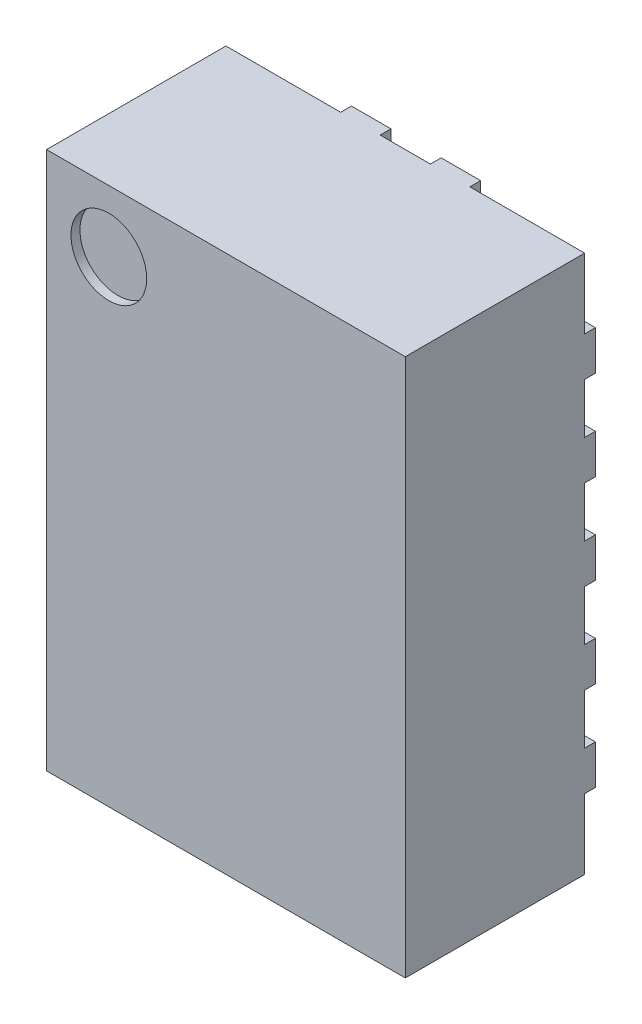
SolidWorks part; units mm, degrees
ref_plane "Front Plane" through (0, 0, 0) normal (0, 0, 1) x (1, 0, 0)
ref_plane "Top Plane" through (0, 0, 0) normal (0, 1, 0) x (1, 0, 0)
ref_plane "Right Plane" through (0, 0, 0) normal (1, 0, 0) x (0, 0, -1)
sketch "Sketch1" plane through (0, 0, 0) normal (0, 0, 1) x (1, 0, 0)
  line L1 (-1, -1.5) -> (1, -1.5)
  line L2 (-1, -1.5) -> (-1, 1.5)
  line L3 (-1, 1.5) -> (1, 1.5)
  line L4 (1, -1.5) -> (1, 1.5)
  line L5 (0, 1.5) -> (0, -1.5) construction
  line L6 (-1, 0) -> (1, 0) construction
  point P0 (0, 0)
  dimension "D1" = 2
  dimension "D2" = 3
extrude "Boss-Extrude1" add sketch "Sketch1" along normal blind 1 from offset 0.06
sketch "Sketch2" plane through (0, 0, 1.06) normal (0, 0, 1) x (1, 0, 0)
  circle A0 centre (-0.653, 1.1551) radius 0.2111
sketch "Sketch3" plane through (0, 0, 0.06) normal (0, 0, -1) x (-1, 0, 0)
  line L0 (1, 0) -> (0.11, 0) construction
  line L1 (1, 1.5) -> (1, -1.5) construction
  line L2 (1, -0.11) -> (0.11, -0.11)
  line L3 (1, 0.11) -> (0.11, 0.11)
  line L4 (1, -0.5) -> (0.45, -0.5) construction
  line L5 (1, -0.61) -> (0.45, -0.61)
  line L6 (1, -0.39) -> (0.45, -0.39)
  line L7 (1, -1) -> (0.6, -1) construction
  line L8 (1, -1.11) -> (0.6, -1.11)
  line L9 (1, -0.89) -> (0.6, -0.89)
  line L10 (1, -1.11) -> (1, -0.89)
  line L11 (1, -0.61) -> (1, -0.39)
  line L12 (1, -0.11) -> (1, 0.11)
  line L13 (-1, 0) -> (-0.45, 0) construction
  line L14 (-1, -1.5) -> (-1, 1.5) construction
  line L15 (-1, 0.11) -> (-0.45, 0.11)
  line L16 (-1, -0.11) -> (-0.45, -0.11)
  line L17 (-1, -0.11) -> (-1, 0.11)
  line L18 (0, 0) -> (0, -1.4452) construction
  line L19 (-1, -0.61) -> (-1, -0.39)
  line L20 (-1, -0.39) -> (-0.45, -0.39)
  line L21 (-1, -0.61) -> (-0.45, -0.61)
  line L22 (-1, -1.11) -> (-1, -0.89)
  line L23 (-1, -0.89) -> (-0.6, -0.89)
  line L24 (-1, -1.11) -> (-0.6, -1.11)
  line L25 (-0.25, -1.5) -> (-0.25, -1.1) construction
  line L26 (1, -1.5) -> (-1, -1.5) construction
  line L27 (-0.36, -1.5) -> (-0.36, -1.1)
  line L28 (-0.14, -1.5) -> (-0.14, -1.1)
  line L29 (-0.36, -1.5) -> (-0.14, -1.5)
  line L30 (0.36, -1.5) -> (0.36, -1.1)
  line L31 (0.36, -1.5) -> (0.14, -1.5)
  line L32 (0.14, -1.5) -> (0.14, -1.1)
  arc A1 (0.11, 0.11) -> (0.11, -0.11) centre (0.11, 0) ccw
  arc A3 (0.45, -0.39) -> (0.45, -0.61) centre (0.45, -0.5) ccw
  arc A5 (0.6, -0.89) -> (0.6, -1.11) centre (0.6, -1) ccw
  arc A7 (-0.45, -0.11) -> (-0.45, 0.11) centre (-0.45, 0) ccw
  arc A8 (-0.45, -0.39) -> (-0.45, -0.61) centre (-0.45, -0.5) cw
  arc A9 (-0.6, -0.89) -> (-0.6, -1.11) centre (-0.6, -1) cw
  arc A11 (-0.14, -1.1) -> (-0.36, -1.1) centre (-0.25, -1.1) ccw
  arc A12 (0.14, -1.1) -> (0.36, -1.1) centre (0.25, -1.1) cw
  point P5 (0.555, 0)
  point P12 (0.725, -0.5)
  point P19 (0.8, -1)
  point P28 (-0.725, 0)
  point P49 (-0.25, -1.3)
  dimension "D4" = 0.55
  dimension "D1" = 0.22
  dimension "D2" = 0.5
  dimension "D3" = 0.22
  dimension "D5" = 0.5
  dimension "D6" = 0.22
  dimension "D7" = 0.4
  dimension "D8" = 0.22
  dimension "D9" = 0.55
  dimension "D10" = 0.22
  dimension "D11" = 0.25
  dimension "D12" = 0.4
extrude "Boss-Extrude2" add sketch "Sketch3" along normal up to surface (0.06 mm away) up to plane "Front Plane"
mirror "Mirror1" about plane through (0, 0, 0) normal (0, 1, 0) of "Boss-Extrude2"
sketch "Sketch4" plane through (0, 0, 0) normal (0, 0, -1) x (-1, 0, 0)
  line L0 (0.673, 1.1318) -> (0.4538, 0.9724)
  line L1 (0.4538, 0.9724) -> (0.4538, 1.1551)
  line L2 (0.4538, 1.1551) -> (0.673, 1.1318)
extrude "Cut-Extrude2" cut sketch "Sketch4" against normal up to surface (0.06 mm away) up to face at (0.0113, 0, 0.06)
extrude "Cut-Extrude3" cut sketch "Sketch2" against normal blind 0.05
